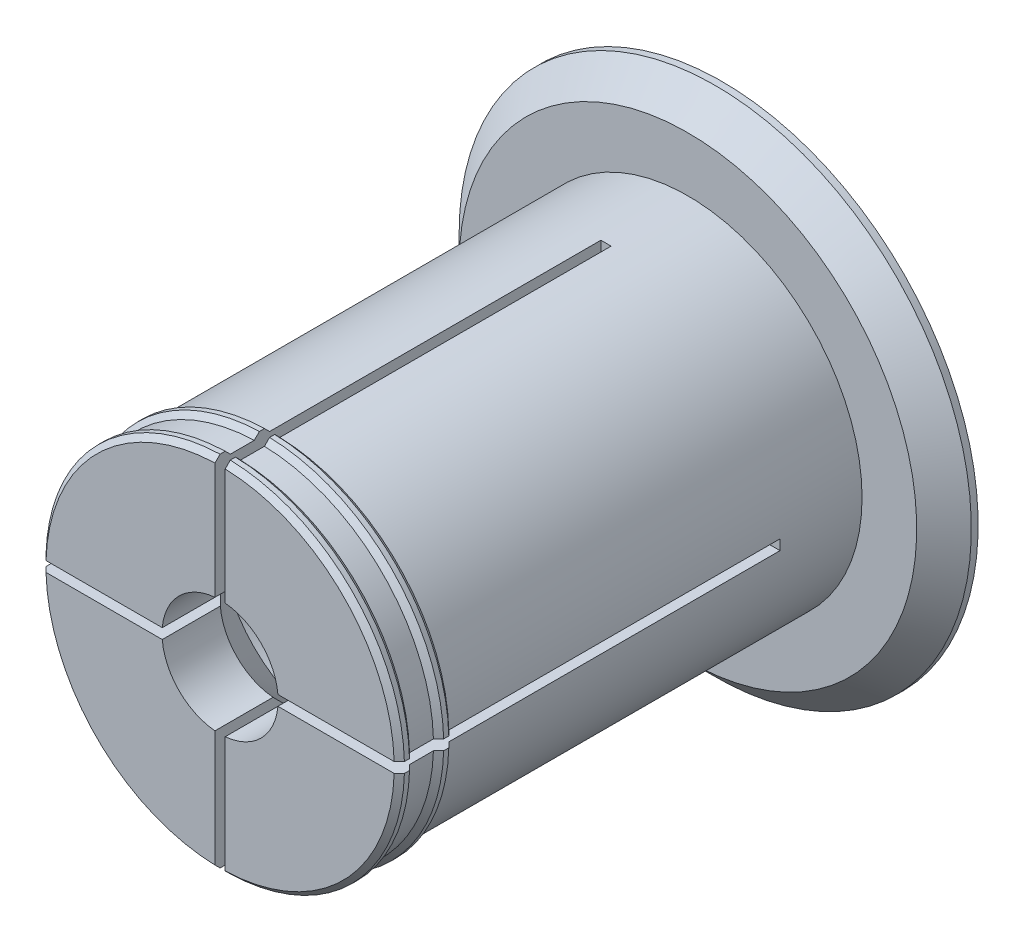
SolidWorks part; units mm, degrees
ref_plane "Front" through (0, 0, 0) normal (0, 0, 1) x (1, 0, 0)
ref_plane "Top" through (0, 0, 0) normal (0, 1, 0) x (1, 0, 0)
ref_plane "Right" through (0, 0, 0) normal (1, 0, 0) x (0, 0, -1)
sketch "Axle base sketch" plane through (0, 0, 0) normal (0, 0, 1) x (1, 0, 0)
  circle A0 centre (0, 0) radius 25.5
  dimension "D1" = 51
extrude "Axle" add sketch "Axle base sketch" along normal blind 68.5
sketch "Guard base" plane through (0, 0, 0) normal (0, 0, -1) x (-1, 0, 0)
  circle A0 centre (0, 0) radius 37.5
  dimension "D1" = 75
extrude "Guard" add sketch "Guard base" along normal blind 5
sketch "Inner axle hole base" plane through (0, 0, 68.5) normal (0, 0, 1) x (1, 0, 0)
  circle A0 centre (0, 0) radius 8.5
  dimension "D1" = 17
extrude "Inner axle hole" cut sketch "Inner axle hole base" against normal through all
sketch "Mate ring base" plane through (0, 0, 0) normal (0, 1, 0) x (1, 0, 0)
  line L0 (25.5, -68.5) -> (26.25, -67.75)
  line L1 (26.25, -67.75) -> (26.25, -67)
  line L2 (26.25, -67) -> (25.5, -66.25)
  line L3 (26.25, -67.75) -> (26.25, -68.5) construction
  line L4 (26.25, -68.5) -> (25.5, -68.5) construction
  line L5 (25.5, -66.25) -> (25.5, -68.5)
  line L6 (25.5, -68.5) -> (25.5, 0) construction
  line L8 (25.5, -62.75) -> (26.25, -62)
  line L9 (26.25, -62) -> (26.25, -61.25)
  line L10 (26.25, -61.25) -> (25.5, -60.5)
  line L11 (25.5, -60.5) -> (25.5, -62.75)
  dimension "D1" = 0.75
  dimension "D2" = 0.75
  dimension "D3" = 5
  dimension "D4" = 0.75
ref_axis "Center Z" through (0, 0, 0) along (0, 0, -1)
revolve "Mate rings" add sketch "Mate ring base" angle 360 about axis through (0, 0, 0) along (0, 0, -1)
sketch "Inner mass remove base" plane through (0, 0, 0) normal (1, 0, 0) x (0, 0, -1)
  line L0 (-68.5, 0) -> (-51.5, -17)
  line L1 (-51.5, -17) -> (-12, -17)
  line L2 (-12, -17) -> (5, 0)
  line L3 (5, 0) -> (-68.5, 0)
  line L4 (5, -8.5) -> (5, 8.5) construction
  line L5 (-51.5, -17) -> (-51.5, -8.5) construction
  line L6 (-51.5, -17) -> (-51.5, -25.5) construction
  line L7 (-68.5, 8.5) -> (-68.5, -8.5) construction
  point P9 (-68.5, -8.5)
  point P11 (-68.5, -25.5)
  dimension "D1" = 135
revolve "Inner mass remove" cut sketch "Inner mass remove base" angle 360 about axis through (0, 0, 0) along (0, 0, -1)
ref_point "Bend room endpoint"
sketch "Bend room base" plane through (0, 0, 68.5) normal (0, 0, 1) x (1, 0, 0)
  line L0 (0.75, -37.5) -> (0.75, 37.5)
  line L1 (0.75, 37.5) -> (-0.75, 37.5)
  line L2 (-0.75, 37.5) -> (-0.75, -37.5)
  line L3 (-0.75, -37.5) -> (0.75, -37.5)
  dimension "D1" = 0.75
  dimension "D2" = 0.75
  dimension "D3" = 37.5
  dimension "D4" = 37.5
extrude "Bend room 1" cut sketch "Bend room base" against normal up to vertex (28.9925 mm away)
pattern_circular "Bend room 2" count 2 every 90 about axis through (0, 0, 0) along (0, 0, -1) of "Bend room 1"
chamfer "Easy removal chamfer" distance 4 angle 45 1 edges at (-37.5, 0, 0)
equation "\"32_92_spool_inner_diameter\"=32"
equation "\"D1@Axle base sketch\"=\"52_62_spool_inner_diameter\"- \"spool_inner_diameter_room\""
equation "\"spool_inner_diameter_room\"=1"
equation "\"32_92_spool_thickness\"=92"
equation "\"D1@Axle\"=\"52_62_spool_thickness\"+\"guard_thickness\"+\"removal_room\"*2"
equation "\"32_92_guard_diameter\"=50"
equation "\"D1@Guard base\"=\"52_62_guard_diameter\""
equation "\"guard_thickness\"=5"
equation "\"D1@Guard\"=\"guard_thickness\""
equation "\"large_inner_axle_diameter\"=20"
equation "\"D1@Inner axle hole base\"=\"small_inner_axle_diameter\""
equation "\"mate_room\"= 0.25"
equation "\"removal_room\"= 0.75"
equation "\"small_inner_axle_diameter\"=17"
equation "\"53_55_spool_inner_diameter\"=53"
equation "\"53_55_spool_thickness\"=55"
equation "\"53_55_guard_diameter\"=75"
equation "\"D1@Mate ring base\"=\"removal_room\""
equation "\"D2@Mate ring base\"=\"removal_room\""
equation "\"D3@Mate ring base\"=\"guard_thickness\""
equation "\"D4@Mate ring base\"=\"removal_room\""
equation "\"D1@Bend room base\" = \"removal_room\""
equation "\"D2@Bend room base\"=\"removal_room\""
equation "\"D3@Bend room base\"=\"52_62_guard_diameter\"/2"
equation "\"D4@Bend room base\"=\"52_62_guard_diameter\"/2"
equation "\"bend_room_length_multiplier\"=3"
equation "\"D1@Easy removal chamfer\"=\"guard_thickness\"-1"
equation "\"32_92_extra_spool_thickness\"=-5"
equation "\"39_92_spool_inner_diameter\"=39"
equation "\"39_92_spool_thickness\"=92"
equation "\"39_92_guard_diameter\"=60"
equation "\"52_62_spool_inner_diameter\"=52"
equation "\"52_62_spool_thickness\"=62"
equation "\"52_62_guard_diameter\"=75"
